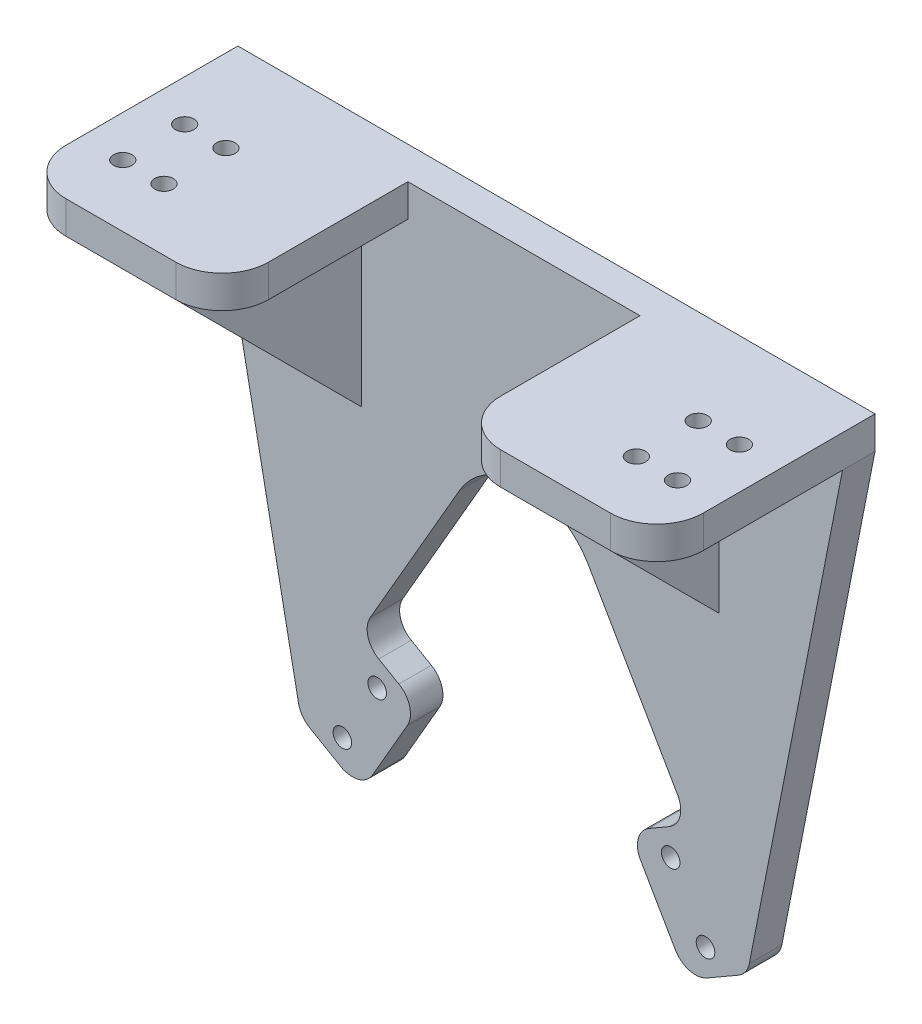
SolidWorks part; units mm, degrees
ref_plane "Front Plane" through (0, 0, 0) normal (0, 0, 1) x (1, 0, 0)
ref_plane "Top Plane" through (0, 0, 0) normal (0, 1, 0) x (1, 0, 0)
ref_plane "Right Plane" through (0, 0, 0) normal (1, 0, 0) x (0, 0, -1)
sketch "Sketch4" plane through (0, 0, 0) normal (0, 0, 1) x (1, 0, 0)
  line L0 (-13.8564, 8) -> (-35.6064, -29.6721)
  line L1 (-35.6064, -29.6721) -> (-22.616, -37.1721)
  line L2 (-22.616, -37.1721) -> (-35.116, -58.8227)
  line L3 (-35.116, -58.8227) -> (-48.1064, -51.3227)
  line L4 (-48.1064, -51.3227) -> (-70, 60)
  line L5 (13.8564, 8) -> (35.6064, -29.6721)
  line L6 (35.6064, -29.6721) -> (22.616, -37.1721)
  line L7 (22.616, -37.1721) -> (35.116, -58.8227)
  line L8 (35.116, -58.8227) -> (48.1064, -51.3227)
  line L9 (48.1064, -51.3227) -> (70, 60)
  line L10 (0, -57.6525) -> (0, 57.6525) construction
  line L11 (-70, 60) -> (70, 60)
  arc A0 (13.8564, 8) -> (-13.8564, 8) centre (0, 0) ccw
  point P20 (0, 60)
  dimension "D4" = 32
  dimension "D1" = 60
  dimension "D2" = 30
  dimension "D3" = 25
  dimension "D5" = 43.5
  dimension "D6" = 15
  dimension "D7" = 140
  dimension "D8" = 60
  dimension "D9" = 25
  dimension "D10" = 15
  dimension "D11" = 43.5
extrude "Boss-Extrude1" add sketch "Sketch4" along normal blind 7
sketch "Sketch5" plane through (0, 0, 0) normal (0, 0, 1) x (1, 0, 0)
  line L0 (0, 16.9972) -> (-39.11, -50.7433) construction
  line L1 (0, -57.6525) -> (0, 57.6525) construction
  line L2 (0, 16.9972) -> (39.11, -50.7433) construction
  line L3 (-28.866, -47.9974) -> (-35.36, -44.2481) construction
  line L4 (-22.616, -37.1721) -> (-35.116, -58.8227) construction
  circle A0 centre (-39.11, -50.7433) radius 2
  circle A1 centre (-31.61, -37.7529) radius 2
  circle A2 centre (39.11, -50.7433) radius 2
  circle A3 centre (31.61, -37.7529) radius 2
  dimension "D7" = 4
  dimension "D8" = 4
  dimension "D9" = 4
  dimension "D10" = 4
  dimension "D1" = 60
  dimension "D2" = 30
  dimension "D3" = 78.22
  dimension "D4" = 78.22
  dimension "D5" = 15
  dimension "D6" = 15
  dimension "D11" = 7.5
extrude "Cut-Extrude2" cut sketch "Sketch5" along normal through all
sketch "Sketch6" plane through (0, 0, 7) normal (0, 0, 1) x (1, 0, 0)
  line L0 (-68.6233, 53) -> (68.6233, 53)
  line L1 (-48.1064, -51.3227) -> (-70, 60) construction
  line L2 (48.1064, -51.3227) -> (70, 60) construction
  line L3 (-70, 60) -> (70, 60) construction
  line L4 (-68.6233, 53) -> (-70, 60)
  line L5 (-70, 60) -> (70, 60)
  line L6 (70, 60) -> (68.6233, 53)
  dimension "D1" = 7
extrude "Boss-Extrude2" add sketch "Sketch6" along normal blind 40
sketch "Sketch7" plane through (0, 0, 47) normal (0, 0, 1) x (1, 0, 0)
  line L0 (-68.6233, 53) -> (-68.6233, 60)
  line L1 (-70, 60) -> (70, 60) construction
  line L2 (-68.6233, 60) -> (-70, 60)
  line L3 (-70, 60) -> (-68.6233, 53)
  line L4 (68.6233, 53) -> (68.6233, 60)
  line L5 (68.6233, 60) -> (70, 60)
  line L6 (70, 60) -> (68.6233, 53)
extrude "Cut-Extrude3" cut sketch "Sketch7" against normal through all
ref_plane "Plane1" through (35, 0, 0) normal (1, 0, 0) x (0, 0, -1)
ref_plane "Plane2" through (-35, 0, 0) normal (-1, 0, 0) x (0, 0, 1)
sketch "Sketch8" plane through (-35, 0, 0) normal (-1, 0, 0) x (0, 0, 1)
  line L0 (7, 13) -> (47, 53)
  line L1 (7, 53) -> (7, -51.3227) construction
  line L2 (47, 53) -> (7, 53)
  line L3 (7, 53) -> (7, 13)
extrude "Boss-Extrude3" add sketch "Sketch8" along normal blind 7
sketch "Sketch9" plane through (35, 0, 0) normal (1, 0, 0) x (0, 0, -1)
  line L0 (-7, 13) -> (-47, 53)
  line L1 (-47, 53) -> (-7, 53)
  line L2 (-7, 53) -> (-7, 13)
extrude "Boss-Extrude4" add sketch "Sketch9" along normal blind 7
fillet "Fillet1" radius 5 8 edges at (-48.1064, -51.3227, 3.5) (48.1064, -51.3227, 3.5) (35.116, -58.8227, 3.5) (22.616, -37.1721, 3.5) (35.6064, -29.6721, 3.5) (-35.6064, -29.6721, 3.5) (-35.116, -58.8227, 3.5) (-22.616, -37.1721, 3.5)
sketch "Sketch10" plane through (0, 60, 0) normal (0, 1, 0) x (1, 0, 0)
  line L0 (-25, -47) -> (-25, -7)
  line L1 (68.6233, -47) -> (-68.6233, -47) construction
  line L2 (-25, -7) -> (25, -7)
  line L3 (25, -7) -> (25, -47)
  line L4 (25, -47) -> (-25, -47)
  line L5 (35, -25.85) -> (35, 25.85) construction
  line L6 (-35, 25.85) -> (-35, -25.85) construction
  line L7 (-65.3525, 0) -> (65.3525, 0) construction
  dimension "D1" = 10
  dimension "D2" = 10
  dimension "D3" = 7
extrude "Cut-Extrude4" cut sketch "Sketch10" against normal through all
fillet "Fillet2" radius 10 4 edges at (68.6233, 56.5, 47) (25, 56.5, 47) (-25, 56.5, 47) (-68.6233, 56.5, 47)
sketch "Sketch11" plane through (0, 53, 0) normal (0, -1, 0) x (1, 0, 0)
  line L0 (-59.7489, 33.6667) -> (-59.7489, 47) construction
  line L1 (-50.8744, 33.6667) -> (-50.8744, 47) construction
  line L2 (-58.6233, 47) -> (-42, 47) construction
  line L3 (-59.7489, 33.6667) -> (-59.7489, 20.3333) construction
  line L4 (-59.7489, 20.3333) -> (-59.7489, 7) construction
  line L5 (-70, 7) -> (70, 7) construction
  line L6 (-50.8744, 33.6667) -> (-50.8744, 20.3333) construction
  line L7 (-50.8744, 20.3333) -> (-50.8744, 7) construction
  line L8 (-68.6233, 33.6667) -> (-59.7489, 33.6667) construction
  line L9 (-68.6233, 37) -> (-68.6233, 7) construction
  line L10 (-59.7489, 33.6667) -> (-50.8744, 33.6667) construction
  line L11 (-50.8744, 33.6667) -> (-42, 33.6667) construction
  line L12 (-42, 47) -> (-42, 7) construction
  line L13 (-68.6233, 20.3333) -> (-59.7489, 20.3333) construction
  line L14 (-59.7489, 20.3333) -> (-50.8744, 20.3333) construction
  line L15 (-50.8744, 20.3333) -> (-42, 20.3333) construction
  line L16 (-42, 7) -> (-42, 47) construction
  line L17 (0, -25.85) -> (0, 25.85) construction
  circle A0 centre (-59.7489, 33.6667) radius 2
  circle A1 centre (-50.8744, 33.6667) radius 2
  circle A2 centre (-59.7489, 20.3333) radius 2
  circle A3 centre (-50.8744, 20.3333) radius 2
  circle A4 centre (50.8744, 20.3333) radius 2
  circle A5 centre (59.7489, 20.3333) radius 2
  circle A6 centre (50.8744, 33.6667) radius 2
  circle A7 centre (59.7489, 33.6667) radius 2
  dimension "D1" = 4
  dimension "D2" = 4
  dimension "D3" = 4
  dimension "D4" = 4
extrude "Cut-Extrude5" cut sketch "Sketch11" against normal through all
equation "\"D5@Sketch4\"=56-12.5"
